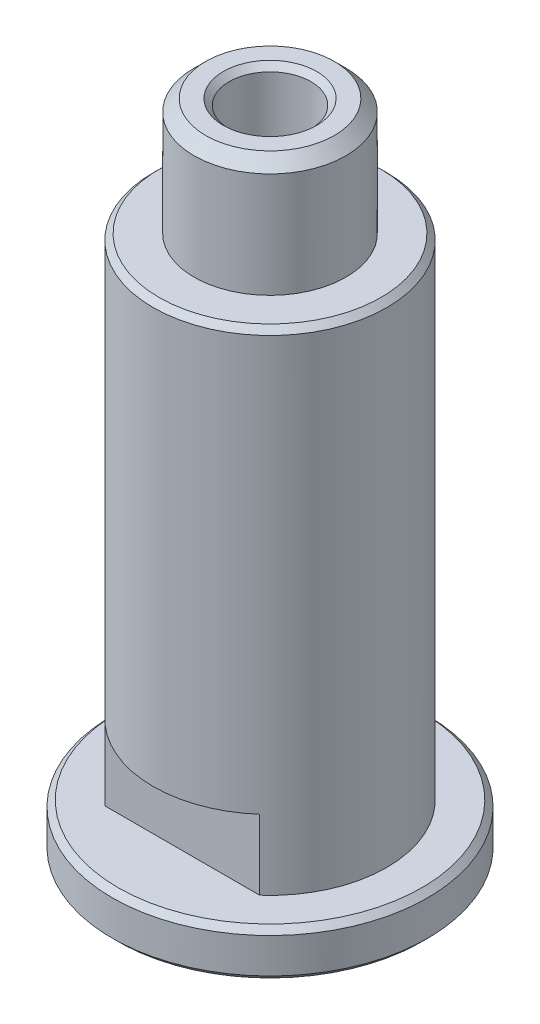
SolidWorks part; units mm, degrees
material "7075-T6 (SN)"
ref_plane "Front Plane" through (0, 0, 0) normal (0, 0, 1) x (1, 0, 0)
ref_plane "Top Plane" through (0, 0, 0) normal (0, 1, 0) x (1, 0, 0)
ref_plane "Right Plane" through (0, 0, 0) normal (1, 0, 0) x (0, 0, -1)
sketch "Sketch1" plane through (0, 0, 0) normal (0, 0, 1) x (1, 0, 0)
  line L0 (0, 0) -> (0, 19.2885) construction
  line L1 (3.5, -5) -> (3.5, 56)
  line L2 (3.5, 56) -> (6.5, 56)
  line L3 (6.5, 56) -> (6.5, 46)
  line L4 (6.5, 46) -> (10, 46)
  line L5 (10, 46) -> (10, 4)
  line L6 (10, 4) -> (13.5, 4)
  line L7 (13.5, 4) -> (13.5, 0)
  line L8 (13.5, 0) -> (6.25, 0)
  line L9 (6.25, 0) -> (6.25, -5)
  line L10 (6.25, -5) -> (3.5, -5)
  dimension "D1" = 13
  dimension "D2" = 7
  dimension "D3" = 10
  dimension "D4" = 5
  dimension "D5" = 12.5
  dimension "D6" = 20
  dimension "D7" = 27
  dimension "D8" = 4
  dimension "D9" = 42
revolve "Revolve1" add sketch "Sketch1" angle 360 about L0
chamfer "Chamfer1" distance 1 angle 45 1 edges at (0, 56, -6.5)
chamfer "Chamfer2" distance 0.5 angle 45 6 edges at (0, 0, -13.5) (0, 4, -13.5) (0, 46, -10) (0, 56, -3.5) (0, -5, -6.25) (0, -5, -3.5)
sketch "Sketch2" plane through (0, 4, 0) normal (0, 1, 0) x (1, 0, 0)
  line L1 (-16.8308, 7.5) -> (16.8308, 7.5)
  line L2 (-16.8308, 7.5) -> (-16.8308, -7.5)
  line L3 (-16.8308, -7.5) -> (16.8308, -7.5)
  line L4 (16.8308, 7.5) -> (16.8308, -7.5)
  line L5 (-16.8308, 7.5) -> (16.8308, -7.5) construction
  line L6 (-16.8308, -7.5) -> (16.8308, 7.5) construction
  point P0 (0, 0)
  dimension "D1" = 15
extrude "Cut-Extrude1" cut sketch "Sketch2" along normal blind 6 flip side to cut
